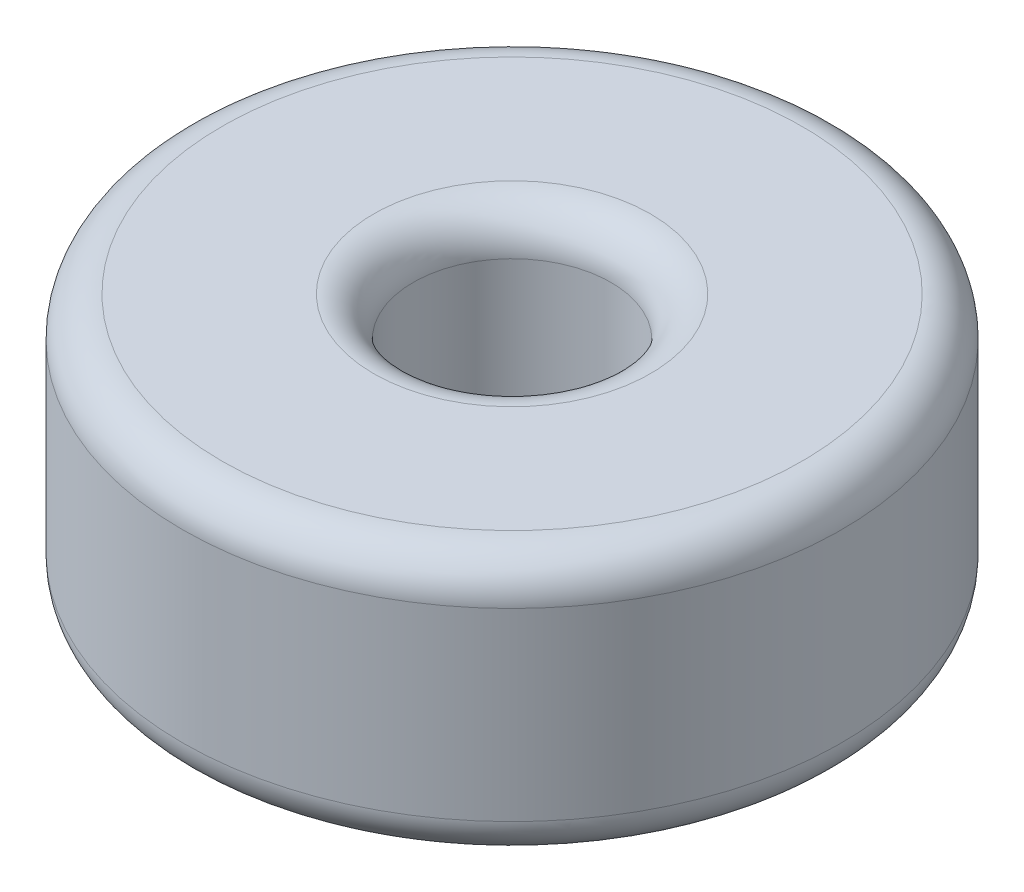
SolidWorks part; units mm, degrees
ref_plane "Front Plane" through (0, 0, 0) normal (0, 0, 1) x (1, 0, 0)
ref_plane "Top Plane" through (0, 0, 0) normal (0, 1, 0) x (1, 0, 0)
ref_plane "Right Plane" through (0, 0, 0) normal (1, 0, 0) x (0, 0, -1)
sketch "Sketch1" plane through (0, 0, 0) normal (0, 1, 0) x (1, 0, 0)
  circle A0 centre (0, 0) radius 5
  circle A1 centre (0, 0) radius 1.5
  dimension "D1" = 10
  dimension "D2" = 3
extrude "Boss-Extrude1" add sketch "Sketch1" along normal blind 4
fillet "Fillet1" radius 0.6 4 edges at (0, 0, 1.5) (0, 0, 5) (0, 4, 1.5) (0, 4, 5)
